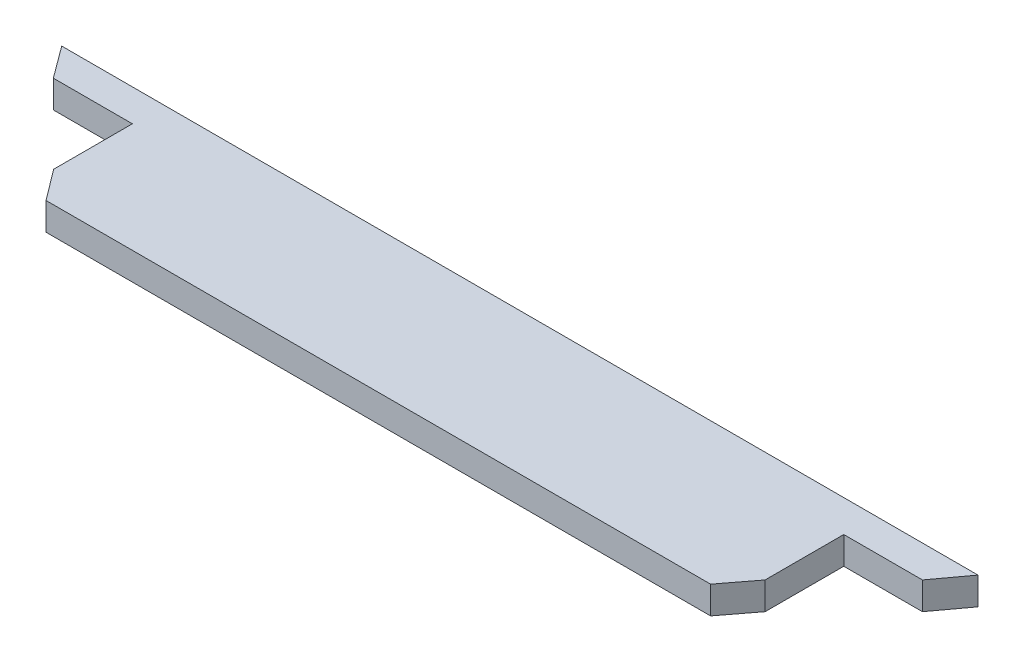
SolidWorks part; units mm, degrees
ref_plane "前视基准面" through (0, 0, 0) normal (0, 0, 1) x (1, 0, 0)
ref_plane "上视基准面" through (0, 0, 0) normal (0, 1, 0) x (1, 0, 0)
ref_plane "右视基准面" through (0, 0, 0) normal (1, 0, 0) x (0, 0, -1)
sketch "草图1" plane through (0, 0, 0) normal (0, 1, 0) x (1, 0, 0)
  line B0 (-1226.0006, 113.6159) -> (1103.9649, 113.6159)
  line B1 (1103.9649, 113.6159) -> (1043.9649, 32.273)
  line B2 (1043.9649, 32.273) -> (843.9649, 32.273)
  line B3 (843.9649, 32.273) -> (843.9649, -167.727)
  line B4 (843.9649, -167.727) -> (783.9649, -246.3841)
  line B5 (783.9649, -246.3841) -> (-906.0006, -246.3841)
  line B6 (-906.0006, -246.3841) -> (-965.0351, -167.727)
  line B7 (-965.0351, -167.727) -> (-965.0351, 32.273)
  line B8 (-965.0351, 32.273) -> (-1166.0006, 32.273)
  line B9 (-1166.0006, 32.273) -> (-1226.0006, 113.6159)
sketch_block_instance "块-Ting-1"
sketch_block "块2"
extrude "凸台-拉伸1" add sketch "草图1" along normal blind 70
